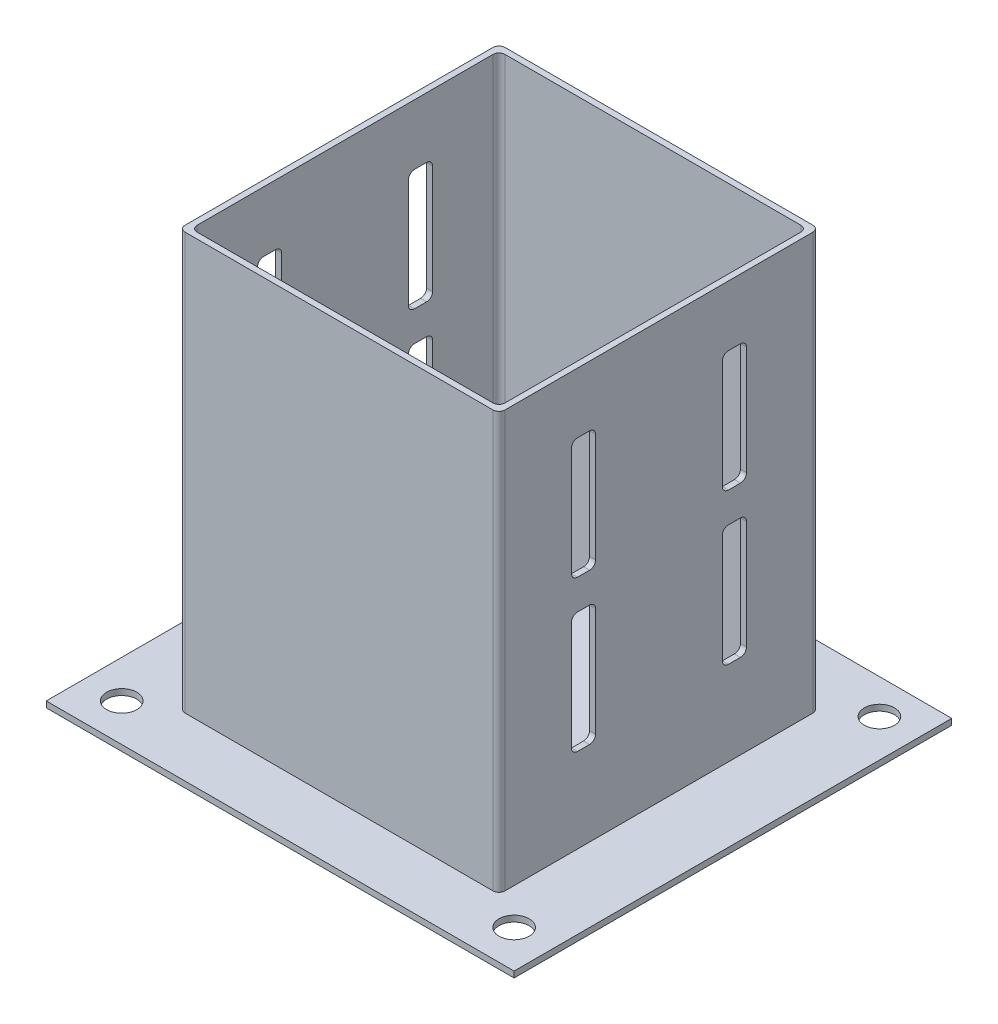
SolidWorks part; units mm, degrees
ref_plane "Front Plane" through (0, 0, 0) normal (0, 0, 1) x (1, 0, 0)
ref_plane "Top Plane" through (0, 0, 0) normal (0, 1, 0) x (1, 0, 0)
ref_plane "Right Plane" through (0, 0, 0) normal (1, 0, 0) x (0, 0, -1)
sketch "Sketch1" plane through (0, 0, 0) normal (0, 1, 0) x (1, 0, 0)
  line L1 (51, -51) -> (-51, -51)
  line L2 (51, -51) -> (51, 51)
  line L3 (51, 51) -> (-51, 51)
  line L4 (-51, -51) -> (-51, 51)
  line L5 (51, -51) -> (-51, 51) construction
  line L6 (51, 51) -> (-51, -51) construction
  line L7 (53, -53) -> (-53, -53)
  line L8 (53, -53) -> (53, 53)
  line L9 (53, 53) -> (-53, 53)
  line L10 (-53, -53) -> (-53, 53)
  line L11 (53, -53) -> (-53, 53) construction
  line L12 (53, 53) -> (-53, -53) construction
  point P0 (0, 0)
  point P6 (0, 0)
  dimension "D1" = 102
  dimension "D2" = 102
  dimension "D3" = 2
  dimension "D4" = 2
extrude "Boss-Extrude1" add sketch "Sketch1" along normal blind 140
sketch "Sketch2" plane through (0, 0, 0) normal (0, 1, 0) x (1, 0, 0)
  line L1 (77.5, -72.5) -> (-77.5, -72.5)
  line L2 (77.5, -72.5) -> (77.5, 72.5)
  line L3 (77.5, 72.5) -> (-77.5, 72.5)
  line L4 (-77.5, -72.5) -> (-77.5, 72.5)
  line L5 (77.5, -72.5) -> (-77.5, 72.5) construction
  line L6 (77.5, 72.5) -> (-77.5, -72.5) construction
  point P0 (0, 0)
  dimension "D1" = 155
  dimension "D2" = 145
extrude "Boss-Extrude2" add sketch "Sketch2" along normal blind 2
sketch "Sketch3" plane through (0, 2, 0) normal (0, 1, 0) x (1, 0, 0)
  line L0 (-65, 61.0402) -> (-65, -60) construction
  line L1 (-65, -60) -> (65, -60) construction
  line L2 (65, -60) -> (65, 61.0402) construction
  line L3 (65, 61.0402) -> (-65, 61.0402) construction
  circle A0 centre (-65, 61.0402) radius 5
  circle A1 centre (65, 61.0402) radius 5
  circle A2 centre (65, -60) radius 5
  circle A3 centre (-65, -60) radius 5
  dimension "D1" = 10
  dimension "D2" = 65
  dimension "D3" = 89.1679
  dimension "D4" = 65
  dimension "D5" = 60
extrude "Cut-Extrude1" cut sketch "Sketch3" against normal blind 2
sketch "Sketch4" plane through (53, 0, 0) normal (1, 0, 0) x (0, 0, -1)
  line L1 (-23, 80) -> (-27, 80)
  line L2 (-21, 82) -> (-21, 118)
  line L3 (-23, 120) -> (-27, 120)
  line L4 (-29, 82) -> (-29, 118)
  line L5 (-21, 80) -> (-29, 120) construction
  line L6 (-21, 120) -> (-29, 80) construction
  arc A0 (-27, 80) -> (-29, 82) centre (-27, 82) cw
  arc A1 (-23, 80) -> (-21, 82) centre (-23, 82) ccw
  arc A2 (-23, 120) -> (-21, 118) centre (-23, 118) cw
  arc A3 (-29, 118) -> (-27, 120) centre (-27, 118) cw
  point P0 (-25, 100)
  point P7 (0, 0)
  point P8 (0, 0)
  dimension "D5" = 2
  dimension "D1" = 8
  dimension "D2" = 40
  dimension "D3" = 25
  dimension "D4" = 100
extrude "Cut-Extrude2" cut sketch "Sketch4" against normal through all both and the other way through all
mirror "Mirror1" about plane through (0, 0, 0) normal (0, 0, 1) of "Cut-Extrude2"
pattern_linear "LPattern1" count 2 spacing 50 along (0, -1, 0) of "Mirror1", "Cut-Extrude2"
fillet "Fillet1" radius 2 8 edges at (51, 71, 51) (53, 71, -53) (-53, 71, -53) (-51, 71, -51) (-51, 71, 51) (51, 71, -51) (53, 71, 53) (-53, 71, 53)
